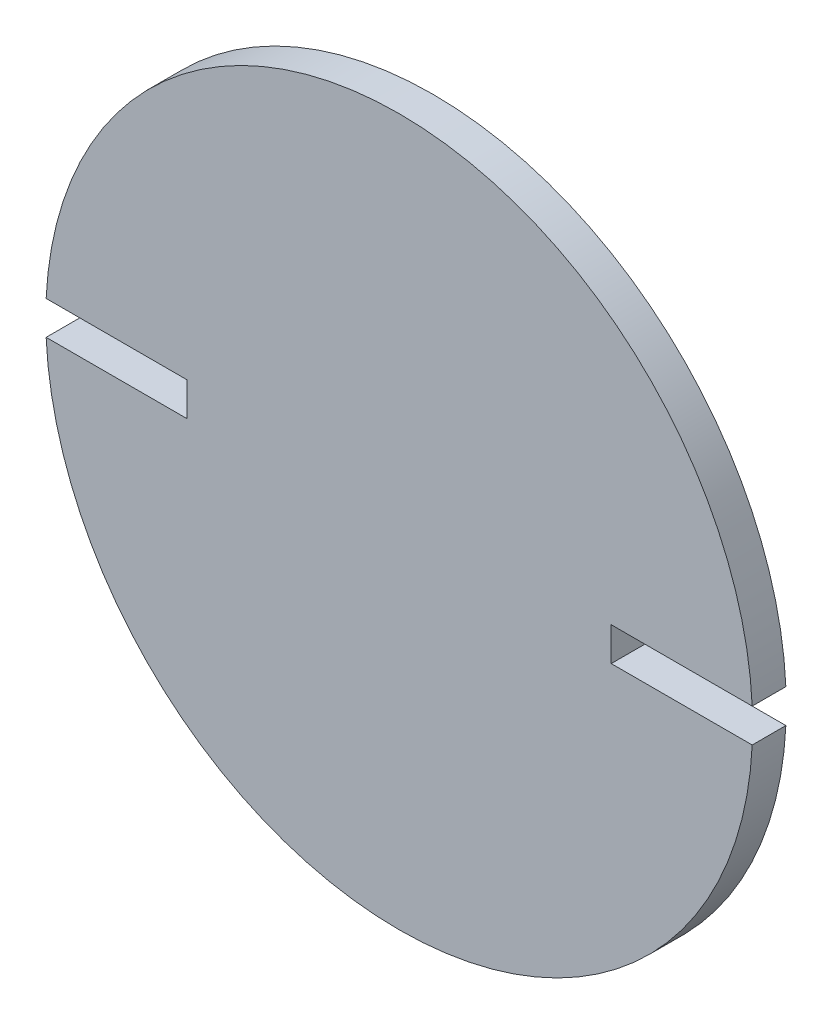
SolidWorks part; units mm, degrees
material "S-Glass Fiber"
ref_plane "Front Plane" through (0, 0, 0) normal (0, 0, 1) x (1, 0, 0)
ref_plane "Top Plane" through (0, 0, 0) normal (0, 1, 0) x (1, 0, 0)
ref_plane "Right Plane" through (0, 0, 0) normal (1, 0, 0) x (0, 0, -1)
sketch "Sketch1" plane through (0, 0, 0) normal (0, 0, 1) x (1, 0, 0)
  circle A0 centre (0, 0) radius 66.675
  dimension "D1" = 133.35
extrude "Boss-Extrude1" add sketch "Sketch1" along normal blind 6.35
sketch "Sketch2" plane through (0, 0, 6.35) normal (0, 0, 1) x (1, 0, 0)
  line L0 (-75.502, 0) -> (76.0599, 0) construction
  line L1 (0, 19.8985) -> (0, -26.0983) construction
  line L2 (-40.005, 0) -> (-40.005, 3.175)
  line L3 (-40.005, 3.175) -> (-67.945, 3.175)
  line L4 (-67.945, 3.175) -> (-67.945, -3.175)
  line L5 (-67.945, -3.175) -> (-40.005, -3.175)
  line L6 (-40.005, -3.175) -> (-40.005, 0)
  line L7 (40.005, -3.175) -> (40.005, 0)
  line L8 (40.005, 0) -> (40.005, 3.175)
  line L9 (67.945, -3.175) -> (40.005, -3.175)
  line L10 (67.945, 3.175) -> (67.945, -3.175)
  line L11 (40.005, 3.175) -> (67.945, 3.175)
  point P8 (-40.005, 1.5875)
  dimension "D1" = 40.005
  dimension "D2" = 6.35
  dimension "D3" = 3.175
  dimension "D4" = 27.94
extrude "Cut-Extrude1" cut sketch "Sketch2" against normal through all
